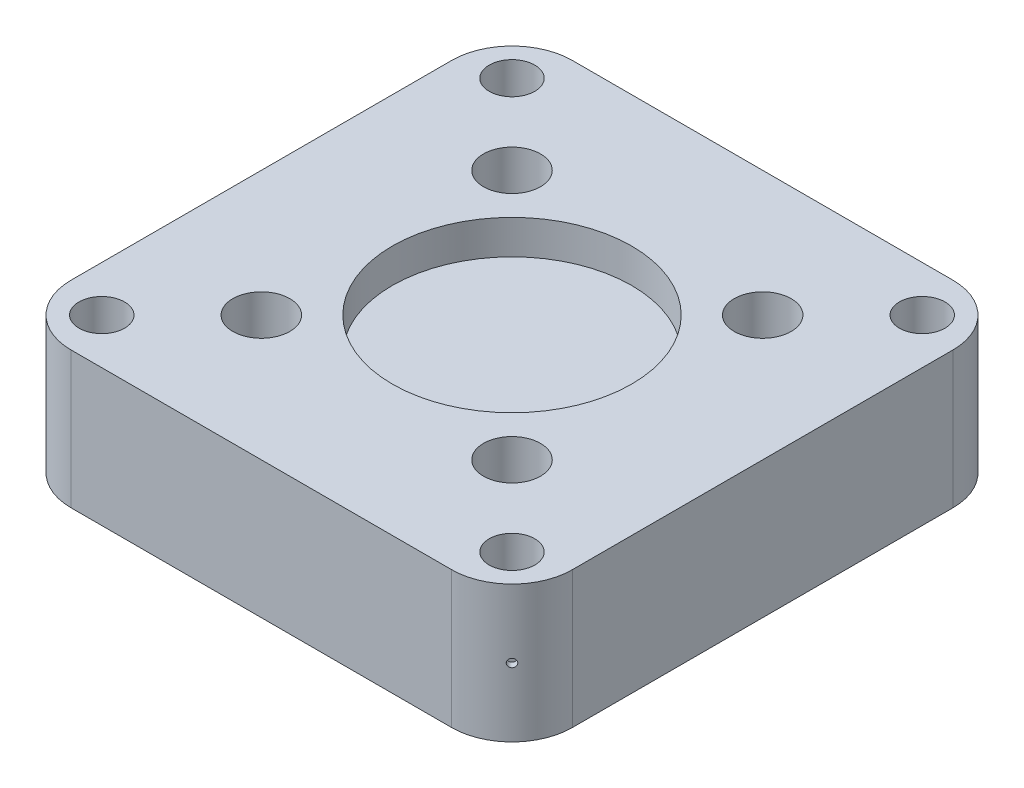
SolidWorks part; units mm, degrees
ref_plane "Front Plane" through (0, 0, 0) normal (0, 0, 1) x (1, 0, 0)
ref_plane "Top Plane" through (0, 0, 0) normal (0, 1, 0) x (1, 0, 0)
ref_plane "Right Plane" through (0, 0, 0) normal (1, 0, 0) x (0, 0, -1)
sketch "Çizim1" plane through (0, 0, 0) normal (0, 1, 0) x (1, 0, 0)
  line L1 (-835, -1100) -> (835, -1100)
  line L2 (-1100, -835) -> (-1100, 835)
  line L3 (-835, 1100) -> (835, 1100)
  line L4 (1100, -835) -> (1100, 835)
  arc A0 (1100, 835) -> (835, 1100) centre (835, 835) ccw
  arc A1 (1100, -835) -> (835, -1100) centre (835, -835) cw
  arc A2 (-1100, -835) -> (-835, -1100) centre (-835, -835) ccw
  arc A3 (-1100, 835) -> (-835, 1100) centre (-835, 835) cw
  circle A4 centre (-900, -900) radius 100
  circle A5 centre (-900, 900) radius 100
  circle A6 centre (900, 900) radius 100
  circle A7 centre (900, -900) radius 100
  circle A8 centre (-550, 550) radius 125
  circle A9 centre (550, 550) radius 125
  circle A10 centre (550, -550) radius 125
  circle A11 centre (-550, -550) radius 125
  point P7 (1100, 1100)
  point P10 (1100, -1100)
  point P13 (-1100, -1100)
  point P16 (-1100, 1100)
  dimension "D5" = 265
  dimension "D6" = 200
  dimension "D14" = 250
  dimension "D19" = 550
  dimension "D1" = 2200
  dimension "D2" = 2200
  dimension "D3" = 1100
  dimension "D4" = 1100
  dimension "D7" = 200
  dimension "D8" = 200
  dimension "D9" = 200
  dimension "D10" = 200
  dimension "D11" = 200
  dimension "D12" = 200
  dimension "D13" = 200
  dimension "D15" = 550
  dimension "D16" = 550
  dimension "D17" = 550
  dimension "D18" = 550
  dimension "D20" = 550
  dimension "D21" = 550
  dimension "D22" = 550
extrude "Yükseklik-Ekstrüzyon3" add sketch "Çizim1" along normal blind 600
sketch "Çizim2" plane through (0, 600, 0) normal (0, 1, 0) x (1, 0, 0)
  circle A0 centre (0, 0) radius 525
extrude "Kes-Ekstrüzyon1" cut sketch "Çizim2" against normal blind 150 contours A0
sketch "Çizim3" plane through (0, 0, 0) normal (0, -1, 0) x (1, 0, 0)
  circle A0 centre (0, 0) radius 400
extrude "Kes-Ekstrüzyon2" cut sketch "Çizim3" against normal blind 200
sketch "Çizim4" plane through (0, 200, 0) normal (0, -1, 0) x (1, 0, 0)
  circle A0 centre (0, 0) radius 400
extrude "Yükseklik-Ekstrüzyon4" add sketch "Çizim4" along normal blind 500
ref_plane "Düzlem1" through (1022.3833, 600, 1022.3833) normal (0.7071, 0, 0.7071) x (0.7071, 0, -0.7071)
sketch "Çizim6" plane through (1022.3833, 600, 1022.3833) normal (0.7071, 0, 0.7071) x (0.7071, 0, -0.7071)
  line L0 (-187.3833, -600) -> (187.3833, -600) construction
  circle A0 centre (0, -300) radius 18
  point P5 (0, -600)
  dimension "D1" = 300
extrude "Kes-Ekstrüzyon3" cut sketch "Çizim6" against normal blind 30
ref_plane "Düzlem2" through (1022.3833, 600, -1022.3833) normal (0.7071, 0, -0.7071) x (-0.7071, 0, -0.7071)
sketch "Çizim8" plane through (1022.3833, 600, -1022.3833) normal (0.7071, 0, -0.7071) x (-0.7071, 0, -0.7071)
  line L0 (-187.3833, -600) -> (187.3833, -600) construction
  circle A0 centre (0, -300) radius 18
  point P4 (0, -600)
  dimension "D1" = 300
extrude "Kes-Ekstrüzyon4" cut sketch "Çizim8" against normal blind 30
ref_plane "Düzlem3" through (-1022.3833, 600, -1022.3833) normal (-0.7071, 0, -0.7071) x (-0.7071, 0, 0.7071)
sketch "Çizim9" plane through (-1022.3833, 600, -1022.3833) normal (-0.7071, 0, -0.7071) x (-0.7071, 0, 0.7071)
  line L0 (-187.3833, -600) -> (187.3833, -600) construction
  circle A0 centre (0, -300) radius 18
  point P4 (0, -600)
  dimension "D1" = 36
  dimension "D2" = 300
extrude "Kes-Ekstrüzyon5" cut sketch "Çizim9" against normal blind 30
ref_plane "Düzlem4" through (-1022.3833, 600, 1022.3833) normal (-0.7071, 0, 0.7071) x (0.7071, 0, 0.7071)
sketch "Çizim10" plane through (-1022.3833, 600, 1022.3833) normal (-0.7071, 0, 0.7071) x (0.7071, 0, 0.7071)
  line L0 (-187.3833, -600) -> (187.3833, -600) construction
  circle A0 centre (0, -300) radius 18
  point P4 (0, -600)
  dimension "D1" = 300
extrude "Kes-Ekstrüzyon6" cut sketch "Çizim10" against normal blind 30
